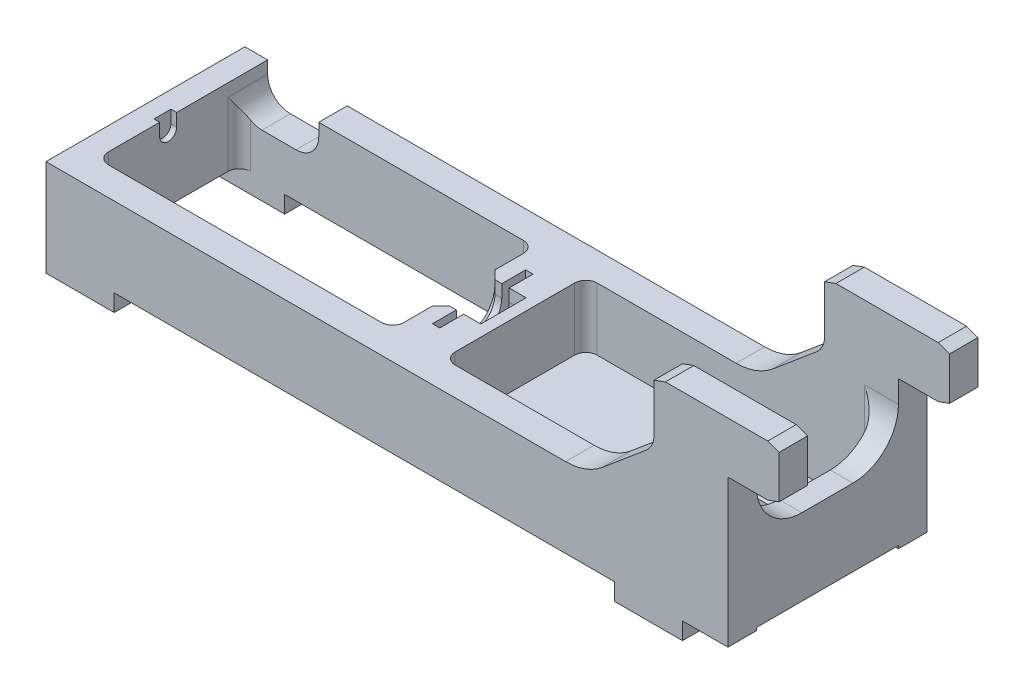
SolidWorks part; units mm, degrees
ref_plane "Front Plane" through (0, 0, 0) normal (0, 0, 1) x (1, 0, 0)
ref_plane "Top Plane" through (0, 0, 0) normal (0, 1, 0) x (1, 0, 0)
ref_plane "Right Plane" through (0, 0, 0) normal (1, 0, 0) x (0, 0, -1)
sketch "Sketch1" plane through (0, 0, 0) normal (0, 0, 1) x (1, 0, 0)
  line L1 (0, 0) -> (60, 0)
  line L2 (0, 0) -> (0, 7)
  line L3 (0, 7) -> (60, 7)
  line L4 (60, 0) -> (60, 7)
  dimension "D1" = 7
  dimension "D2" = 60
extrude "Boss-Extrude1" add sketch "Sketch1" along normal mid plane 17.5
sketch "Sketch2" plane through (0, 7, 0) normal (0, 1, 0) x (1, 0, 0)
  line L0 (0, -8.75) -> (0, 8.75) construction
  line L1 (2, 6.25) -> (28, 6.25)
  line L2 (2, 6.25) -> (2, -6.25)
  line L3 (2, -6.25) -> (28, -6.25)
  line L4 (28, 6.25) -> (28, -6.25)
  line L5 (2, 0) -> (0, 0) construction
  dimension "D1" = 26
  dimension "D2" = 2
  dimension "D3" = 12.5
extrude "Cut-Extrude1" cut sketch "Sketch2" against normal through all
sketch "Sketch3" plane through (0, 0, 0) normal (0, 0, 1) x (1, 0, 0)
  line L0 (0, 5.9) -> (36.2319, 5.9) construction
  line L1 (0, 0) -> (60, 0) construction
  line L2 (1.5, 5.9) -> (1.5, 5.15)
  line L3 (1.5, 5.15) -> (28, 5.15)
  line L4 (29.35, 3.9) -> (29.35, 1.8)
  line L5 (29.35, 1.8) -> (30, 1.8)
  line L6 (30, 1.8) -> (30, 3.9)
  line L7 (30, 3.9) -> (31.5, 3.9)
  line L8 (31.5, 3.9) -> (31.5, 5.9)
  line L9 (31.5, 5.9) -> (1.5, 5.9)
  line L10 (0, 7) -> (0, 0) construction
  line L11 (2, 0) -> (2, 7) construction
  line L12 (28, 5.15) -> (28, 3.9)
  line L14 (28, 3.9) -> (29.35, 3.9)
  line L16 (28, 0) -> (28, 7) construction
  dimension "D1" = 5.9
  dimension "D2" = 0.75
  dimension "D3" = 0.5
  dimension "D4" = 2
  dimension "D5" = 27.85
  dimension "D6" = 0.65
  dimension "D7" = 1.5
  dimension "D8" = 4.1
revolve "Cut-Revolve5" cut sketch "Sketch3" angle 360 about L0
sketch "Sketch4" plane through (28, 0, 0) normal (-1, 0, 0) x (0, 0, 1)
  line L0 (8.75, 7) -> (-8.75, 7) construction
  line L1 (-2, 5.9) -> (2, 5.9)
  line L2 (-2, 5.9) -> (-2, 7)
  line L3 (-2, 7) -> (2, 7)
  line L4 (2, 5.9) -> (2, 7)
  circle A0 centre (0, 5.9) radius 2 construction
extrude "Cut-Extrude2" cut sketch "Sketch4" against normal up to surface (3.5 mm away) up to face at (31.5, 5.45, 0)
sketch "Sketch5" plane through (29.35, 0, 0) normal (1, 0, 0) x (0, 0, -1)
  line L0 (-8.75, 7) -> (8.75, 7) construction
  line L1 (-4.1, 5.9) -> (4.1, 5.9)
  line L2 (-4.1, 5.9) -> (-4.1, 7)
  line L3 (-4.1, 7) -> (4.1, 7)
  line L4 (4.1, 5.9) -> (4.1, 7)
  arc A0 (-3.9497, 7) -> (3.9497, 7) centre (0, 5.9) ccw construction
extrude "Cut-Extrude4" cut sketch "Sketch5" along normal up to surface (0.65 mm away) up to face at (30, 5.4333, 0)
sketch "Sketch6" plane through (2, 0, 0) normal (1, 0, 0) x (0, 0, -1)
  line L0 (-8.75, 7) -> (8.75, 7) construction
  line L1 (-0.75, 5.9) -> (0.75, 5.9)
  line L2 (-0.75, 5.9) -> (-0.75, 7)
  line L3 (-0.75, 7) -> (0.75, 7)
  line L4 (0.75, 5.9) -> (0.75, 7)
  circle A0 centre (0, 5.9) radius 0.75 construction
extrude "Cut-Extrude5" cut sketch "Sketch6" against normal up to surface (0.5 mm away) up to face at (1.5, 5.9, 0.75)
sketch "Sketch7" plane through (0, 0, 8.75) normal (0, 0, 1) x (1, 0, 0)
  line L0 (54.5, 17.4625) -> (53.5, 17.0985)
  line L1 (63.5, 12.9625) -> (64.5, 13.3265)
  line L2 (54.5, 17.4625) -> (63.5, 17.4625)
  line L3 (63.5, 17.4625) -> (64.5, 17.0985)
  line L4 (64.5, 17.0985) -> (64.5, 13.3265)
  line L5 (63.5, 12.9625) -> (60, 12.9625)
  line L6 (60, 12.9625) -> (60, 7)
  line L7 (63.5, 12.9625) -> (63.5, 17.4625) construction
  line L8 (63.5, 15.2125) -> (64.5, 15.2125) construction
  line L9 (16.5897, 12.7) -> (63.4333, 12.7) construction
  line L10 (0, 0) -> (60, 0) construction
  line L11 (53.5, 17.0985) -> (53.5, 12)
  line L12 (53.5, 12) -> (47.5412, 7)
  line L13 (60, 7) -> (0, 7) construction
  line L14 (47.5412, 7) -> (60, 7)
  dimension "D1" = 12.7
  dimension "D2" = 4.7625
  dimension "D3" = 20
  dimension "D4" = 4.5
  dimension "D5" = 4.5
  dimension "D6" = 1
  dimension "D7" = 12
  dimension "D8" = 40
  dimension "D9" = 11
extrude "Boss-Extrude2" add sketch "Sketch7" against normal blind 2.5
sketch "Sketch9" plane through (0, 0, 0) normal (0, -1, 0) x (1, 0, 0)
  line L0 (0, 8.75) -> (60, 8.75) construction
  line L1 (0, 8.75) -> (6, 8.75)
  line L2 (0, 8.75) -> (0, 6.25)
  line L3 (0, 6.25) -> (6, 6.25)
  line L4 (6, 8.75) -> (6, 6.25)
  line L5 (2, 6.25) -> (28, 6.25) construction
  line L9 (50, 8.75) -> (56, 8.75)
  line L10 (50, 8.75) -> (50, 6.25)
  line L11 (50, 6.25) -> (56, 6.25)
  line L12 (56, 8.75) -> (56, 6.25)
  dimension "D2" = 6
  dimension "D3" = 50
extrude "Boss-Extrude4" add sketch "Sketch9" along normal blind 1.5
mirror "Mirror1" about plane through (0, 0, 0) normal (0, 0, 1) of "Boss-Extrude4", "Boss-Extrude2"
sketch "Sketch10" plane through (0, 7, 0) normal (0, 1, 0) x (1, 0, 0)
  line L0 (63.5, 6.25) -> (54.5, 6.25) construction
  line L1 (58, 6.25) -> (32.5, 6.25)
  line L2 (58, 6.25) -> (58, -6.25)
  line L3 (58, -6.25) -> (32.5, -6.25)
  line L4 (32.5, 6.25) -> (32.5, -6.25)
  line L5 (63.5, -6.25) -> (54.5, -6.25) construction
  line L6 (60, -6.25) -> (60, 6.25) construction
  line L7 (31.5, -2) -> (31.5, 2) construction
  dimension "D1" = 2
  dimension "D2" = 1
extrude "Cut-Extrude6" cut sketch "Sketch10" against normal offset from surface (5.5 mm away) 1.5 up to face at (36.8125, 0, -0.0781)
sketch "Sketch11" plane through (0, 1.5, 0) normal (0, 1, 0) x (1, 0, 0)
  line L0 (52.35, 0) -> (48.35, 0) construction
  line L1 (52.35, -2.3813) -> (48.35, -2.3813)
  line L2 (52.35, 2.3812) -> (48.35, 2.3813)
  line L3 (29.35, -2) -> (29.35, 2) construction
  arc A0 (52.35, -2.3813) -> (52.35, 2.3812) centre (52.35, 0) ccw
  arc A1 (48.35, 2.3813) -> (48.35, -2.3813) centre (48.35, 0) ccw
  point P2 (50.35, 0)
  dimension "D1" = 4.7625
  dimension "D2" = 4
  dimension "D3" = 19
extrude "Cut-Extrude7" cut sketch "Sketch11" against normal through all
sketch "Sketch12" plane through (0, 0, 0) normal (0, -1, 0) x (1, 0, 0)
  line L0 (60, 8.75) -> (60, -8.75) construction
  line L1 (0, 6.25) -> (60, 6.25)
  line L2 (0, 6.25) -> (0, -6.25)
  line L3 (0, -6.25) -> (60, -6.25)
  line L4 (60, 6.25) -> (60, -6.25)
  line L5 (50, -6.25) -> (56, -6.25) construction
extrude "Cut-Extrude8" cut sketch "Sketch12" against normal blind 0.25
fillet "Fillet1" radius 4 2 edges at (59, 7, -6.25)
fillet "Fillet2" radius 5 2 edges at (47.5412, 7, -7.5)
fillet "Fillet3" radius 1 8 edges at (32.5, 4.25, -6.25) (32.5, 4.25, 6.25) (58, 6.25, 6.25) (58, 6.25, -6.25) (28, 3.625, 6.25) (28, 3.625, -6.25) (2, 3.625, -6.25)
sketch "Sketch13" plane through (0, 0, -8.75) normal (0, 0, -1) x (-1, 0, 0)
  line L0 (-45.7214, 7) -> (0, 7) construction
  line L1 (-2, 7) -> (-2, 5.9)
  line L2 (-9, 7) -> (-2, 7)
  line L3 (-29.35, 5.9) -> (-28, 5.9) construction
  line L4 (-2, 0.25) -> (-2, 7) construction
  line L5 (-4, 3.9) -> (-7, 3.9)
  line L6 (-9, 5.9) -> (-9, 7)
  arc A1 (-4, 3.9) -> (-2, 5.9) centre (-4, 5.9) ccw
  arc A2 (-7, 3.9) -> (-9, 5.9) centre (-7, 5.9) cw
  dimension "D2" = 2
  dimension "D1" = 3
extrude "Cut-Extrude9" cut sketch "Sketch13" against normal blind 10
fillet "Fillet4" radius 2 2 edges at (53.5, 12, -7.5) (53.5, 12, 7.5)
chamfer "Chamfer1" distance 0.75 angle 45 3 edges at (28, 6.45, 2) (28, 6.45, -2) (28, 3.9, 0)
